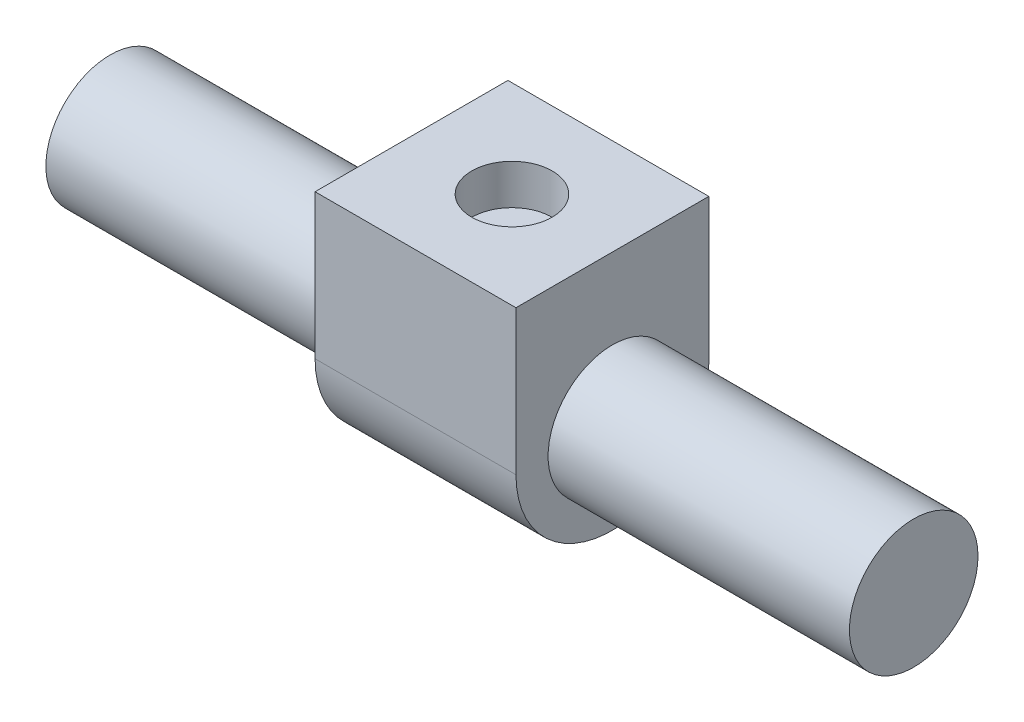
SolidWorks part; units mm, degrees
ref_plane "Front Plane" through (0, 0, 0) normal (0, 0, 1) x (1, 0, 0)
ref_plane "Top Plane" through (0, 0, 0) normal (0, 1, 0) x (1, 0, 0)
ref_plane "Right Plane" through (0, 0, 0) normal (1, 0, 0) x (0, 0, -1)
sketch "Sketch1" plane through (0, 0, 0) normal (1, 0, 0) x (0, 0, -1)
  line L2 (-12, 0) -> (-12, 18)
  line L3 (-12, 18) -> (12, 18)
  line L4 (12, 0) -> (12, 18)
  arc A0 (-12, 0) -> (12, 0) centre (0, 0) ccw
  dimension "D1" = 24
  dimension "D2" = 18
extrude "Boss-Extrude1" add sketch "Sketch1" along normal mid plane 25
sketch "Sketch2" plane through (0, 0, 0) normal (1, 0, 0) x (0, 0, -1)
  circle A0 centre (0, 0) radius 8
  dimension "D1" = 16
extrude "Boss-Extrude2" add sketch "Sketch2" along normal mid plane 100
sketch "Sketch3" plane through (0, 18, 0) normal (0, 1, 0) x (1, 0, 0)
  circle A0 centre (0, 0) radius 5
  dimension "D1" = 10
extrude "Cut-Extrude1" cut sketch "Sketch3" against normal blind 5
